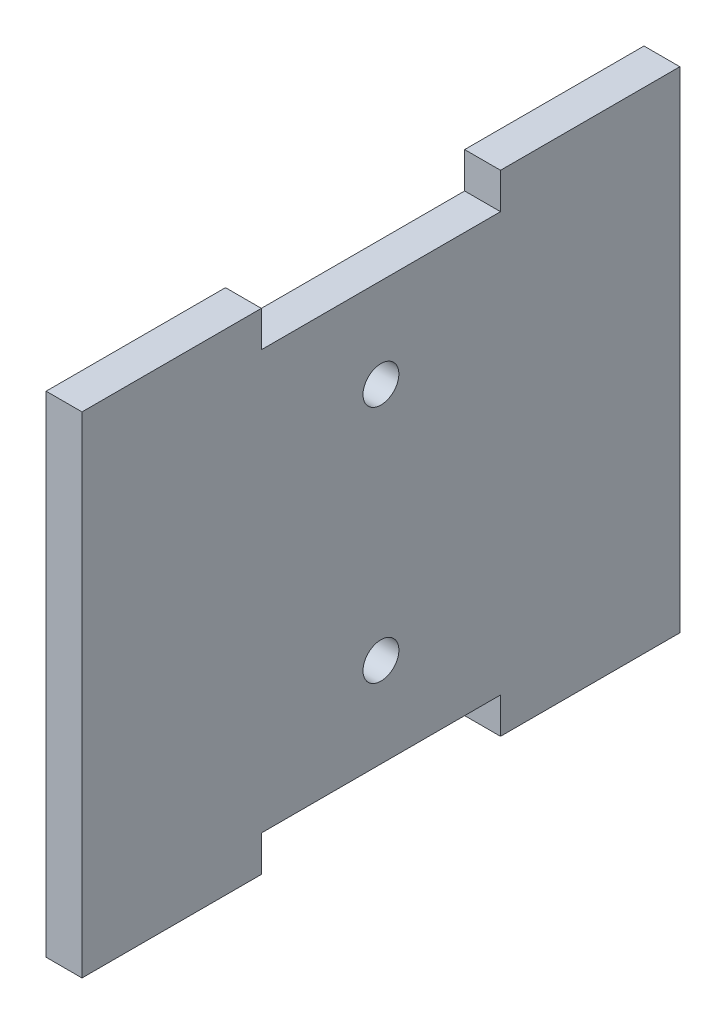
SolidWorks part; units mm, degrees
ref_plane "前视基准面" through (0, 0, 0) normal (0, 0, 1) x (1, 0, 0)
ref_plane "上视基准面" through (0, 0, 0) normal (0, 1, 0) x (1, 0, 0)
ref_plane "右视基准面" through (0, 0, 0) normal (1, 0, 0) x (0, 0, -1)
sketch "草图1" plane through (0, 0, 0) normal (1, 0, 0) x (0, 0, -1)
  line L0 (-10, 17.5) -> (10, 17.5)
  line L1 (0, 0) -> (25, 0) construction
  line L2 (0, -17.5) -> (0, 17.5) construction
  line L3 (10, 20.5) -> (25, 20.5)
  line L4 (25, -20.5) -> (25, 20.5)
  line L5 (10, 17.5) -> (10, 20.5)
  line L6 (-25, -20.5) -> (-25, 20.5)
  line L7 (-10, 17.5) -> (-10, 20.5)
  line L8 (-10, 20.5) -> (-25, 20.5)
  line L15 (-10, -20.5) -> (-25, -20.5)
  line L16 (-10, -17.5) -> (-10, -20.5)
  line L17 (10, -17.5) -> (10, -20.5)
  line L18 (10, -20.5) -> (25, -20.5)
  line L23 (-10, -17.5) -> (10, -17.5)
  circle A0 centre (0, -10) radius 1.5
  circle A1 centre (0, 10) radius 1.5
  point P8 (17.5, 20.5)
  point P9 (10, 19)
  point P10 (12.5, 0)
  point P21 (-25, 0)
  dimension "D5" = 3
  dimension "D1" = 3
  dimension "D2" = 20
  dimension "D3" = 41
  dimension "D4" = 10
  dimension "D6" = 50
extrude "凸台-拉伸1" add sketch "草图1" along normal blind 3
